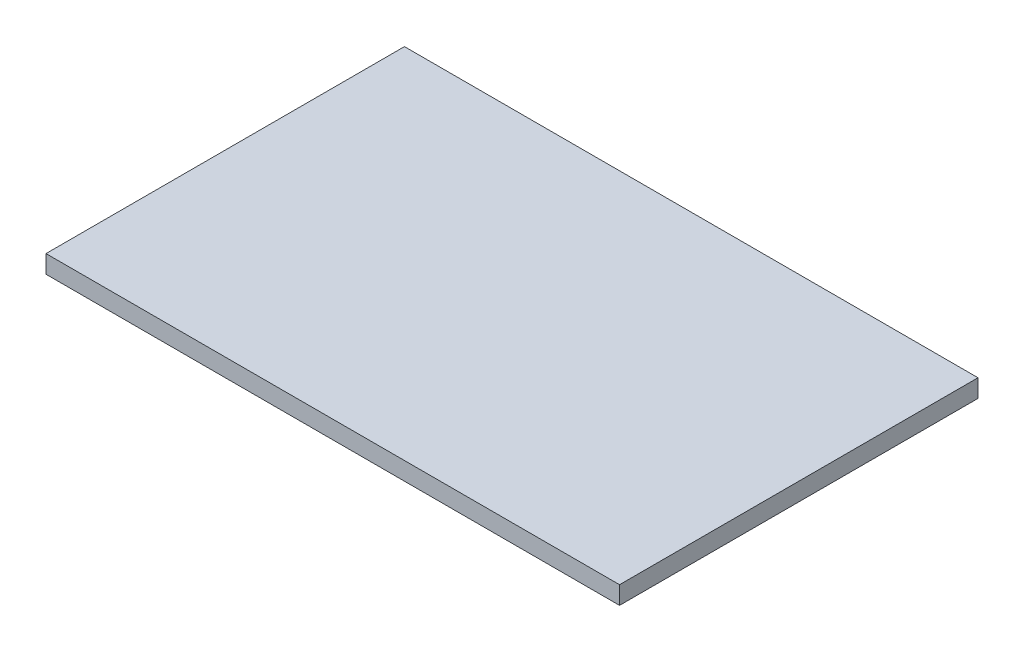
SolidWorks part; units mm, degrees
ref_plane "Front Plane" through (0, 0, 0) normal (0, 0, 1) x (1, 0, 0)
ref_plane "Top Plane" through (0, 0, 0) normal (0, 1, 0) x (1, 0, 0)
ref_plane "Right Plane" through (0, 0, 0) normal (1, 0, 0) x (0, 0, -1)
sketch "Sketch1" plane through (0, 0, 0) normal (0, 1, 0) x (1, 0, 0)
  line L1 (112.6, 79.3333) -> (-47.4, 79.3333)
  line L2 (112.6, 79.3333) -> (112.6, -20.6667)
  line L3 (112.6, -20.6667) -> (-47.4, -20.6667)
  line L4 (-47.4, 79.3333) -> (-47.4, -20.6667)
extrude "Boss-Extrude1" add sketch "Sketch1" along normal blind 5
